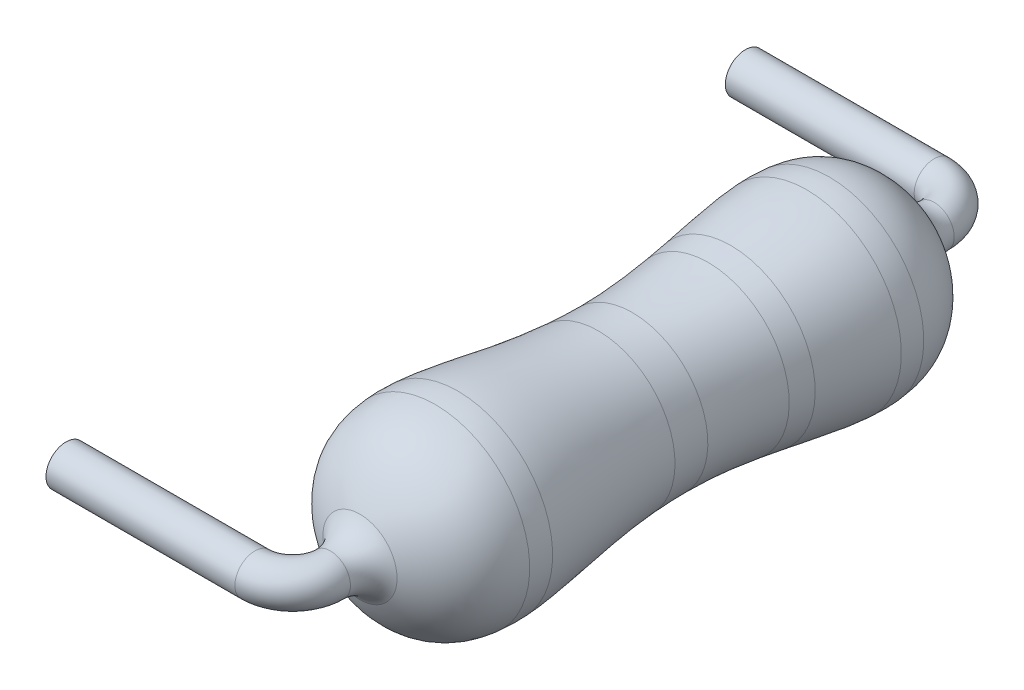
SolidWorks part; units mm, degrees
ref_plane "Front Plane" through (0, 0, 0) normal (0, 0, 1) x (1, 0, 0)
ref_plane "Top Plane" through (0, 0, 0) normal (0, 1, 0) x (1, 0, 0)
ref_plane "Right Plane" through (0, 0, 0) normal (1, 0, 0) x (0, 0, -1)
sketch "Sketch1" plane through (0, 0, 0) normal (1, 0, 0) x (0, 0, -1)
  line L0 (0, -1.25) -> (0, 1.25)
  line L1 (-3.5, 0.265) -> (3.5, 0.265)
  line L2 (-3.5, 0.265) -> (-3.5, -0.265)
  line L3 (-3.5, -0.265) -> (3.5, -0.265)
  line L4 (3.5, 0.265) -> (3.5, -0.265)
  line L5 (-3.5, 0.265) -> (3.5, -0.265) construction
  line L6 (-3.5, -0.265) -> (3.5, 0.265) construction
  line L7 (-3.4, -0.265) -> (-3.4, 0.265)
  line L8 (3.4, 0.265) -> (3.4, -0.265)
  line L14 (-3.4, 0.265) -> (-3.4, 1.25) construction
  line L15 (-3.4, 1.25) -> (3.4, 1.25) construction
  line L16 (-3.5, 0) -> (3.5, 0) construction
  line L17 (3.4, 1.25) -> (3.4, 0.265) construction
  point P0 (0, 0)
  point P5 (-3.4, 0)
  point P6 (3.4, 0)
  point P15 (0, 0)
  point P28 (-2.9038, 0)
  point P29 (-3.9963, 0)
  point P30 (2.9037, 0)
  point P31 (3.9962, 0)
  dimension "Wire Diameter" = 0.53
  dimension "Wire Length" = 0.1
  dimension "D1" = 0.1
  dimension "Body Length" = 6.8
  dimension "Body Diameter" = 2.5
  dimension "D6" = 0.5963
  dimension "D7" = 0.5962
  dimension "D8" = 0.5962
  dimension "D9" = 0.5962
sketch "Sketch2" plane through (0, 0, 0) normal (1, 0, 0) x (0, 0, -1)
  line L0 (-3.5, 0) -> (3.5, 0)
  line L1 (-3.5, 0.265) -> (-3.5, -0.265) construction
  line L2 (3.5, 0.265) -> (3.5, -0.265) construction
  line L3 (3.5, 0) -> (3.5, 0.265)
  line L4 (3.5, 0.265) -> (-3.5, 0.265)
  line L5 (-3.5, 0.265) -> (-3.5, 0)
revolve "Revolve1" add sketch "Sketch2" angle 360 about L0
sketch "Sketch3" plane through (0, 0, 0) normal (1, 0, 0) x (0, 0, -1)
  line L0 (-3.4, 0) -> (-3.4, 1.25) construction
  line L1 (-3.4, 1.25) -> (3.4, 1.25) construction
  line L2 (3.4, 1.25) -> (3.4, 0) construction
  line L3 (3.4, 0) -> (-3.4, 0) construction
  line L4 (-3.6981, 0.265) -> (3.6981, 0.265)
  line L5 (-3.6981, 0.265) -> (-2.6083, 3.2593) construction
  line L6 (-2.6083, 3.2593) -> (0, -1.7673) construction
  line L7 (0, -1.7673) -> (2.6083, 3.2593) construction
  line L8 (2.6083, 3.2593) -> (3.6981, 0.265) construction
  line L9 (0, -1.25) -> (0, 1.25) construction
  line L10 (-2.6083, 3.2593) -> (2.6083, 3.2593) construction
  line L11 (-2.6083, 3.2593) -> (-2.6083, 1.25) construction
  line L12 (0, 1.25) -> (0, 1) construction
  line L13 (-3.5, 0.265) -> (3.5, 0.265) construction
  line L14 (-3.9963, 0) -> (-3.4, 0) construction
  line L15 (-3.6981, 0) -> (-3.6981, 0.265) construction
  line L16 (3.4, 0) -> (3.9962, 0) construction
  line L17 (3.6981, 0.265) -> (3.6981, 0) construction
  spline S0 degree 4 poles (-3.6981, 0.265) (-2.6083, 3.2593) (0, -1.7673) (2.6083, 3.2593) (3.6981, 0.265) knots 0 0 0 0 0 1 1 1 1 1
  dimension "D1" = 20
  dimension "D2" = 2
revolve "Revolve2" add sketch "Sketch3" angle 360 about L3
sketch "Sketch4" plane through (0, 0, 0) normal (1, 0, 0) x (0, 0, -1)
  line L0 (-3.9963, 0.265) -> (3.9962, 0.265)
  line L1 (-3.5, 0.265) -> (3.5, 0.265) construction
  line L2 (3.605, 0.4909) -> (-3.605, 0.4909)
  line L3 (-3.9963, 0.265) -> (-3.9963, 0) construction
  line L4 (-3.9963, 0) -> (3.9962, 0) construction
  line L5 (3.9962, 0) -> (3.9962, 0.265) construction
  line L6 (-3.9963, 0.265) -> (-3.605, 0.4909) construction
  arc A0 (3.9962, 0.265) -> (3.605, 0.4909) centre (3.9962, 0.7168) cw
  arc A1 (-3.9963, 0.265) -> (-3.605, 0.4909) centre (-3.9963, 0.7168) ccw
  spline S0 degree 4 poles (3.6981, 0.265) (2.6083, 3.2593) (0, -1.7673) (-2.6083, 3.2593) (-3.6981, 0.265) knots 0 0 0 0 0 1 1 1 1 1 construction
  dimension "D1" = 30
revolve "Revolve3" add sketch "Sketch4" angle 360 about L4
sketch "Sketch5" plane through (0, 0, 0) normal (1, 0, 0) x (0, 0, -1)
  line L5 (-2.6083, 1.5) -> (-2.6083, -1.5)
  line L6 (-2.3083, -1.5) -> (-2.3083, 1.5)
  line L7 (2.6083, 1.5) -> (2.6083, -1.5)
  line L8 (2.3083, -1.5) -> (2.3083, 1.5)
  line L9 (-2.6083, 3.2593) -> (-2.6083, 1.25) construction
  line L10 (0, -1.5) -> (0, 1.5)
  line L11 (-0.45, 1.5) -> (-0.45, -1.5)
  line L12 (1.0042, -1.5) -> (1.0042, 1.5)
  line L13 (1.3042, 1.5) -> (1.3042, -1.5)
  line L14 (0, 0) -> (1.0042, 0) construction
  line L15 (-3.5, 0.265) -> (3.5, -0.265) construction
  line L16 (1.3042, 0) -> (2.3083, 0) construction
  line L17 (-3.5, 0) -> (3.5, 0) construction
  line L18 (-3.4, 1.5) -> (3.4, 1.5) construction
  line L19 (-3.4, 1.5) -> (-3.4, -1.5) construction
  line L20 (-3.4, -1.5) -> (3.4, -1.5) construction
  line L21 (3.4, 1.5) -> (3.4, -1.5) construction
  dimension "D1" = 0.3
  dimension "D2" = 0.3
  dimension "D3" = 0.3
  dimension "D4" = 0.45
  dimension "D5" = 3
split line "Split Line1"
sketch "Sketch6" plane through (0, 0, 0) normal (0, 1, 0) x (1, 0, 0)
  line L0 (0, 3.9962) -> (0, -3.9963)
  line L1 (-0.5, -4.4963) -> (-3, -4.4963)
  line L4 (-0.5, 4.4962) -> (-3, 4.4962)
  line L7 (0.265, 3.9962) -> (-0.265, 3.9962) construction
  line L8 (0.265, -3.9963) -> (-0.265, -3.9963) construction
  arc A0 (0, 3.9962) -> (-0.5, 4.4962) centre (-0.5, 3.9962) ccw
  arc A1 (0, -3.9963) -> (-0.5, -4.4963) centre (-0.5, -3.9963) cw
  point P3 (0, 0)
  point P6 (0, 0)
  point P7 (0, -5.3112)
  point P8 (0, 0)
  point P9 (0, 0)
  point P11 (0, 0)
  point P15 (0, -4.4963)
  point P16 (0, 0)
  point P19 (0, 0)
  point P21 (0, 0)
  point P22 (0, 3.5)
  point P24 (0, 0)
  dimension "D2" = 0.5
  dimension "D1" = 3
sketch "Sketch7" plane through (0, 0, 0) normal (0, 0, 1) x (1, 0, 0)
  circle A0 centre (0, 0) radius 0.265
  circle A1 centre (0, 0) radius 0.265 construction
sweep "Sweep1" add profiles "Sketch7" path "Sketch6"
equation "\"D1@Sketch1\" = \"Wire Length@Sketch1\""
equation "\"D6@Sketch1\"=\"Wire Diameter@Sketch1\"*1.125"
equation "\"D7@Sketch1\"=\"D6@Sketch1\""
equation "\"D8@Sketch1\"=\"D6@Sketch1\""
equation "\"D9@Sketch1\"=\"D8@Sketch1\""
equation "\"D2@Sketch3\"=\"Body Diameter@Sketch1\"*.8"
equation "\"D1@Sketch5\"=\"Body Diameter@Sketch1\"*.12"
equation "\"D2@Sketch5\"=\"D1@Sketch5\""
equation "\"D3@Sketch5\"=\"D1@Sketch5\""
equation "\"D4@Sketch5\"=\"D1@Sketch5\"*1.5"
equation "\"D1@Sketch4\"=\"D1@Sketch3\"*1.5"
equation "\"D5@Sketch5\"=\"Body Diameter@Sketch1\"*1.2"
